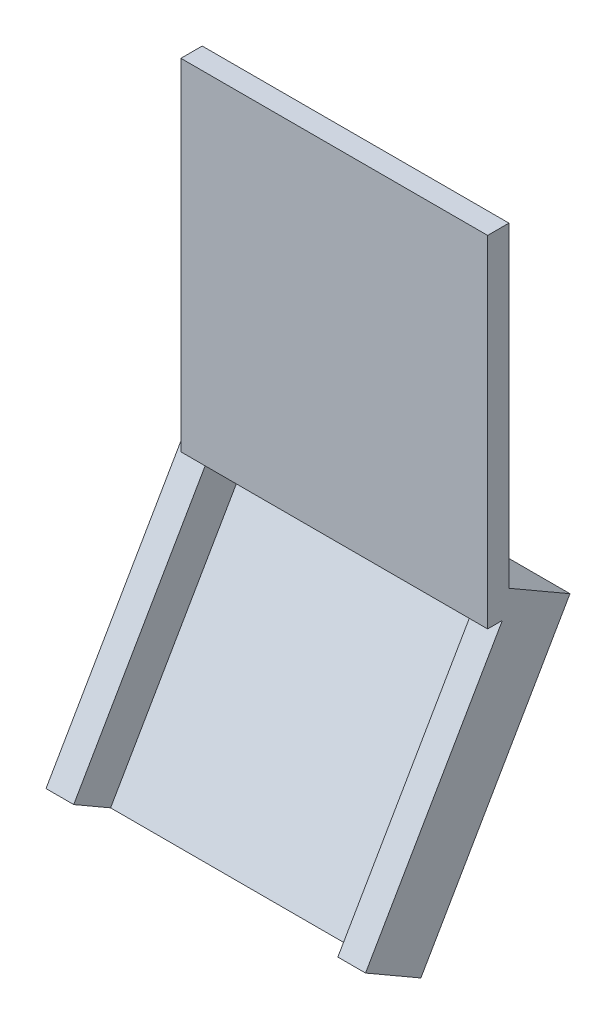
SolidWorks part; units mm, degrees
material "ABS"
ref_plane "Ebene vorne" through (0, 0, 0) normal (0, 0, 1) x (1, 0, 0)
ref_plane "Ebene oben" through (0, 0, 0) normal (0, 1, 0) x (1, 0, 0)
ref_plane "Ebene rechts" through (0, 0, 0) normal (1, 0, 0) x (0, 0, -1)
sketch "Skizze1" plane through (0, 0, 0) normal (0, 0, 1) x (1, 0, 0)
  line L1 (0, 0) -> (14.4, 0)
  line L2 (0, 0) -> (0, 16)
  line L3 (0, 16) -> (14.4, 16)
  line L4 (14.4, 0) -> (14.4, 16)
  dimension "D1" = 14.4
  dimension "D2" = 16
extrude "Aufsatz-Linear austragen1" add sketch "Skizze1" along normal blind 1
sketch "Skizze4" plane through (14.4, 0, 0) normal (1, 0, 0) x (0, 0, -1)
  line L0 (-1, 0) -> (2, 0) construction
  line L1 (2, 0) -> (0, 1.1547)
  line L2 (0, 0) -> (0, 16) construction
  line L3 (2, 0) -> (-5, -12.1244)
  line L4 (2, 0) -> (2.866, -0.5)
  line L5 (2.866, -0.5) -> (-4.134, -12.6244)
  line L6 (-4.134, -12.6244) -> (-5, -12.1244)
  line L7 (1.5, -0.866) -> (0, 0)
  dimension "D1" = 1
  dimension "D2" = 14
  dimension "D3" = 30
  dimension "D4" = 14
  dimension "D5" = 3
  dimension "D6" = 1
extrude "Aufsatz-Linear austragen4" add sketch "Skizze4" against normal blind 15
sketch "Skizze9" plane through (0, -0.866, -1.5) normal (0, 0.5, 0.866) x (1, 0, 0)
  line L0 (-0.6, -13) -> (14.4, -13) construction
  line L1 (14.4, 0) -> (13.1, 0)
  line L2 (14.4, 0) -> (14.4, -13)
  line L3 (14.4, -13) -> (13.1, -13)
  line L4 (13.1, 0) -> (13.1, -13)
  line L7 (-0.6, 0) -> (0.7, 0)
  line L9 (-0.6, 0) -> (-0.6, -13)
  line L10 (-0.6, -13) -> (0.7, -13)
  line L11 (0.7, 0) -> (0.7, -13)
  dimension "D1" = 1.3
  dimension "D2" = 1.3
extrude "Aufsatz-Linear austragen5" add sketch "Skizze9" along normal blind 2
